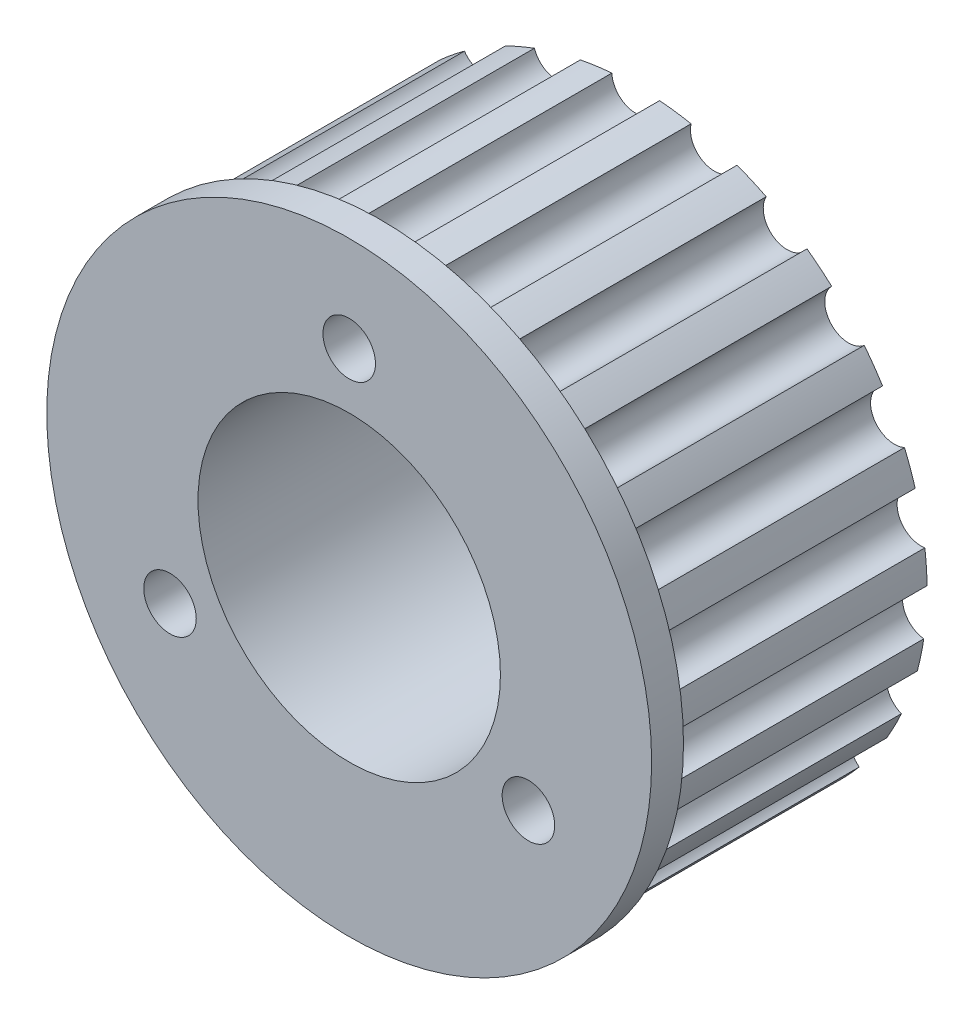
SolidWorks part; units mm, degrees
ref_plane "Спереди" through (0, 0, 0) normal (0, 0, 1) x (1, 0, 0)
ref_plane "Сверху" through (0, 0, 0) normal (0, 1, 0) x (1, 0, 0)
ref_plane "Справа" through (0, 0, 0) normal (1, 0, 0) x (0, 0, -1)
sketch "Эскиз1" plane through (0, 0, 0) normal (0, 0, 1) x (1, 0, 0)
  arc A0 (-1.4987, 18.2415) -> (-3.4783, 17.9694) centre (0, 0) ccw
  circle A1 centre (0, 0) radius 9.5
  arc A2 (-1.4987, 18.2415) -> (1.4987, 18.2415) centre (0, 18.303) ccw
  arc A3 (3.4783, 17.9694) -> (6.3647, 17.1607) centre (4.9381, 17.6243) ccw
  arc A4 (8.1975, 16.3646) -> (10.7586, 14.8072) centre (9.5099, 15.6384) ccw
  arc A5 (12.3086, 13.5462) -> (14.3545, 11.3555) centre (13.3765, 12.4928) ccw
  arc A6 (15.5069, 9.723) -> (16.8859, 7.0616) centre (16.251, 8.4206) ccw
  arc A7 (17.5551, 5.1787) -> (18.1649, 2.244) centre (17.9202, 3.7239) ccw
  arc A8 (18.3013, 0.2504) -> (18.0967, -2.7401) centre (18.2603, -1.249) ccw
  arc A9 (17.6902, -4.6965) -> (16.6864, -7.5209) centre (17.2462, -6.1293) ccw
  arc A10 (15.7671, -9.2951) -> (14.0385, -11.744) centre (14.953, -10.555) ccw
  arc A11 (12.6746, -13.2043) -> (10.3494, -15.096) centre (11.5508, -14.1978) ccw
  arc A12 (8.6421, -16.1342) -> (5.8928, -17.3284) centre (7.2919, -16.7877) ccw
  arc A13 (3.9687, -17.8676) -> (0.9991, -18.2757) centre (2.4923, -18.1325) ccw
  arc A14 (-0.9991, -18.2757) -> (-3.9687, -17.8676) centre (-2.4923, -18.1325) ccw
  arc A15 (-5.8928, -17.3284) -> (-8.6421, -16.1342) centre (-7.2919, -16.7877) ccw
  arc A16 (-10.3494, -15.096) -> (-12.6746, -13.2043) centre (-11.5508, -14.1978) ccw
  arc A17 (-14.0385, -11.744) -> (-15.7671, -9.2951) centre (-14.953, -10.555) ccw
  arc A18 (-16.6864, -7.5209) -> (-17.6902, -4.6965) centre (-17.2462, -6.1293) ccw
  arc A19 (-18.0967, -2.7401) -> (-18.3013, 0.2504) centre (-18.2603, -1.249) ccw
  arc A20 (-18.1649, 2.244) -> (-17.5551, 5.1787) centre (-17.9202, 3.7239) ccw
  arc A21 (-18.1649, 2.244) -> (-18.3013, 0.2504) centre (0, 0) ccw
  arc A22 (-18.0967, -2.7401) -> (-17.6902, -4.6965) centre (0, 0) ccw
  arc A23 (-16.6864, -7.5209) -> (-15.7671, -9.2951) centre (0, 0) ccw
  arc A24 (-14.0385, -11.744) -> (-12.6746, -13.2043) centre (0, 0) ccw
  arc A25 (-10.3494, -15.096) -> (-8.6421, -16.1342) centre (0, 0) ccw
  arc A26 (-5.8928, -17.3284) -> (-3.9687, -17.8676) centre (0, 0) ccw
  arc A27 (-0.9991, -18.2757) -> (0.9991, -18.2757) centre (0, 0) ccw
  arc A28 (3.9687, -17.8676) -> (5.8928, -17.3284) centre (0, 0) ccw
  arc A29 (8.6421, -16.1342) -> (10.3494, -15.096) centre (0, 0) ccw
  arc A30 (12.6746, -13.2043) -> (14.0385, -11.744) centre (0, 0) ccw
  arc A31 (15.7671, -9.2951) -> (16.6864, -7.5209) centre (0, 0) ccw
  arc A32 (17.6902, -4.6965) -> (18.0967, -2.7401) centre (0, 0) ccw
  arc A33 (18.3013, 0.2504) -> (18.1649, 2.244) centre (0, 0) ccw
  arc A34 (17.5551, 5.1787) -> (16.8859, 7.0616) centre (0, 0) ccw
  arc A35 (15.5069, 9.723) -> (14.3545, 11.3555) centre (0, 0) ccw
  arc A36 (12.3086, 13.5462) -> (10.7586, 14.8072) centre (0, 0) ccw
  arc A37 (8.1975, 16.3646) -> (6.3647, 17.1607) centre (0, 0) ccw
  arc A38 (3.4783, 17.9694) -> (1.4987, 18.2415) centre (0, 0) ccw
  arc A39 (-16.8859, 7.0616) -> (-15.5069, 9.723) centre (-16.251, 8.4206) ccw
  arc A40 (-14.3545, 11.3555) -> (-12.3086, 13.5462) centre (-13.3765, 12.4928) ccw
  arc A41 (-10.7586, 14.8072) -> (-8.1975, 16.3646) centre (-9.5099, 15.6384) ccw
  arc A42 (-6.3647, 17.1607) -> (-3.4783, 17.9694) centre (-4.9381, 17.6243) ccw
  arc A43 (-6.3647, 17.1607) -> (-8.1975, 16.3646) centre (0, 0) ccw
  arc A44 (-10.7586, 14.8072) -> (-12.3086, 13.5462) centre (0, 0) ccw
  arc A45 (-14.3545, 11.3555) -> (-15.5069, 9.723) centre (0, 0) ccw
  arc A46 (-16.8859, 7.0616) -> (-17.5551, 5.1787) centre (0, 0) ccw
  point P63 (0, 0)
  dimension "D1" = 36.606
  dimension "D2" = 19
  dimension "D3" = 3
  dimension "D4" = 23
extrude "Бобышка-Вытянуть1" add sketch "Эскиз1" along normal blind 16
sketch "Эскиз2" plane through (0, 0, 16) normal (0, 0, 1) x (1, 0, 0)
  circle A0 centre (0, 0) radius 9.5
  circle A1 centre (0, 0) radius 19
  circle A2 centre (0, 0) radius 9.5 construction
  dimension "D1" = 38
extrude "Бобышка-Вытянуть2" add sketch "Эскиз2" along normal blind 2
sketch "Эскиз4" plane through (0, 0, 18) normal (0, 0, 1) x (1, 0, 0)
  line L0 (-11.2583, -6.5) -> (11.2583, -6.5) construction
  line L1 (11.2583, -6.5) -> (0, 13) construction
  line L2 (0, 13) -> (-11.2583, -6.5) construction
  line L3 (0, 13) -> (0, -6.5) construction
  line L4 (11.2583, -6.5) -> (-5.6292, 3.25) construction
  circle A0 centre (0, 13) radius 1.65
  circle A1 centre (11.2583, -6.5) radius 1.65
  circle A2 centre (-11.2583, -6.5) radius 1.65
  circle A3 centre (0, 0) radius 13
  point P11 (0, 0)
  dimension "D1" = 26
  dimension "D2" = 3.3
extrude "Вырез-Вытянуть1" cut sketch "Эскиз4" against normal through all contours A3 A2 | A2 A3 | A3 A0 | A0 A3 | A3 A1 | A1 A3
